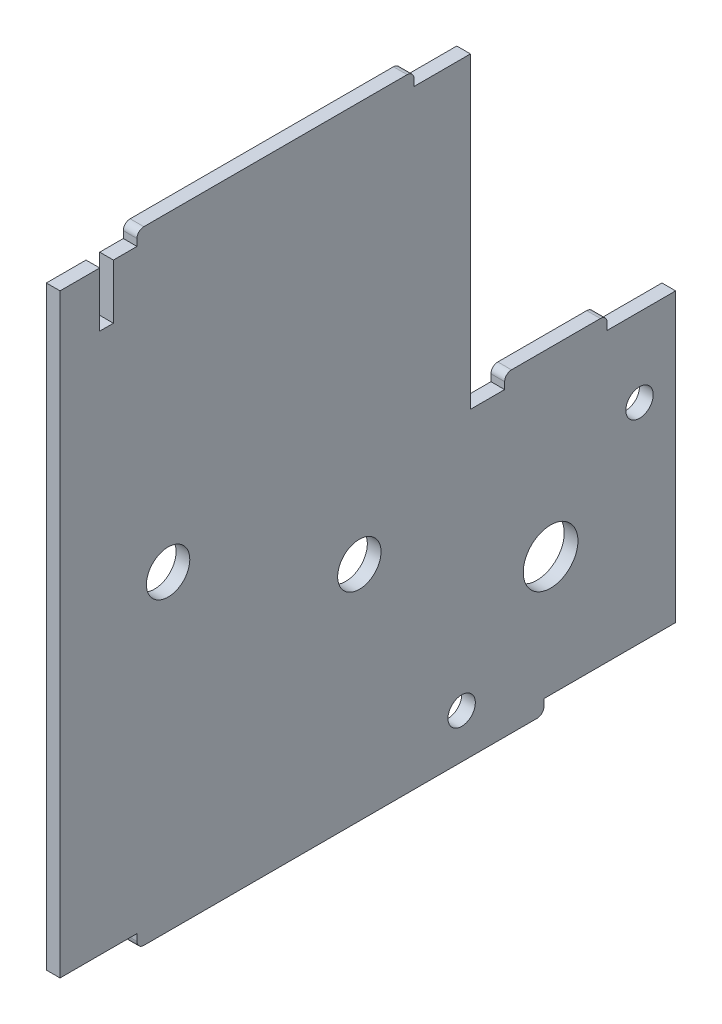
SolidWorks part; units mm, degrees
ref_plane "Front Plane" through (0, 0, 0) normal (0, 0, 1) x (1, 0, 0)
ref_plane "Top Plane" through (0, 0, 0) normal (0, 1, 0) x (1, 0, 0)
ref_plane "Right Plane" through (0, 0, 0) normal (1, 0, 0) x (0, 0, -1)
sketch "Sketch1" plane through (0, 0, 0) normal (1, 0, 0) x (0, 0, -1)
  line L1 (54.5194, -39.9699) -> (54.5194, 2.0301)
  line L2 (24.5194, 2.0301) -> (24.5194, 47.0301)
  line L3 (43.5194, 4.0301) -> (30.5194, 4.0301)
  line L4 (-24.2301, -39.9699) -> (-24.2301, -40.9699)
  line L5 (-27.6806, 47.0301) -> (-24.2301, 47.0301)
  line L6 (54.5194, -39.9699) -> (35.2689, -39.9699)
  line L7 (-35.4806, -39.9699) -> (-24.2301, -39.9699)
  line L8 (54.5194, 2.0301) -> (44.5194, 2.0301)
  line L9 (29.5194, 2.0301) -> (29.5194, 3.0301)
  line L10 (15.2689, 49.0301) -> (-23.2301, 49.0301)
  line L11 (35.2689, -39.9699) -> (35.2689, -40.9699)
  line L12 (44.5194, 2.0301) -> (44.5194, 3.0301)
  line L13 (29.5194, 2.0301) -> (24.5194, 2.0301)
  line L14 (16.2689, 47.0301) -> (24.5194, 47.0301)
  line L15 (-24.2301, 47.0301) -> (-24.2301, 48.0301)
  line L16 (-23.2301, -41.9699) -> (34.2689, -41.9699)
  line L17 (16.2689, 47.0301) -> (16.2689, 48.0301)
  line L18 (-35.4806, -39.9699) -> (-35.4806, 47.0301)
  line L19 (-27.6806, 39.0301) -> (-29.6806, 39.0301)
  line L20 (-27.6806, 39.0301) -> (-27.6806, 47.0301)
  line L21 (-29.6806, 47.0301) -> (-35.4806, 47.0301)
  line L22 (-29.6806, 39.0301) -> (-29.6806, 47.0301)
  arc A0 (-23.2301, -41.9699) -> (-24.2301, -40.9699) centre (-23.2301, -40.9699) cw
  arc A1 (44.5194, 3.0301) -> (43.5194, 4.0301) centre (43.5194, 3.0301) ccw
  circle A2 centre (36.2338, -22.4699) radius 4
  arc A3 (29.5194, 3.0301) -> (30.5194, 4.0301) centre (30.5194, 3.0301) cw
  arc A4 (34.2689, -41.9699) -> (35.2689, -40.9699) centre (34.2689, -40.9699) ccw
  arc A5 (16.2689, 48.0301) -> (15.2689, 49.0301) centre (15.2689, 48.0301) ccw
  arc A6 (-24.2301, 48.0301) -> (-23.2301, 49.0301) centre (-23.2301, 48.0301) cw
  circle A8 centre (49.2338, -9.4699) radius 2
  circle A10 centre (23.2338, -35.4699) radius 2
  circle A11 centre (-19.6806, 3.5301) radius 3.17
  circle A12 centre (8.2766, -9.4699) radius 3.17
extrude "Boss-Extrude1" add sketch "Sketch1" along normal blind 2
